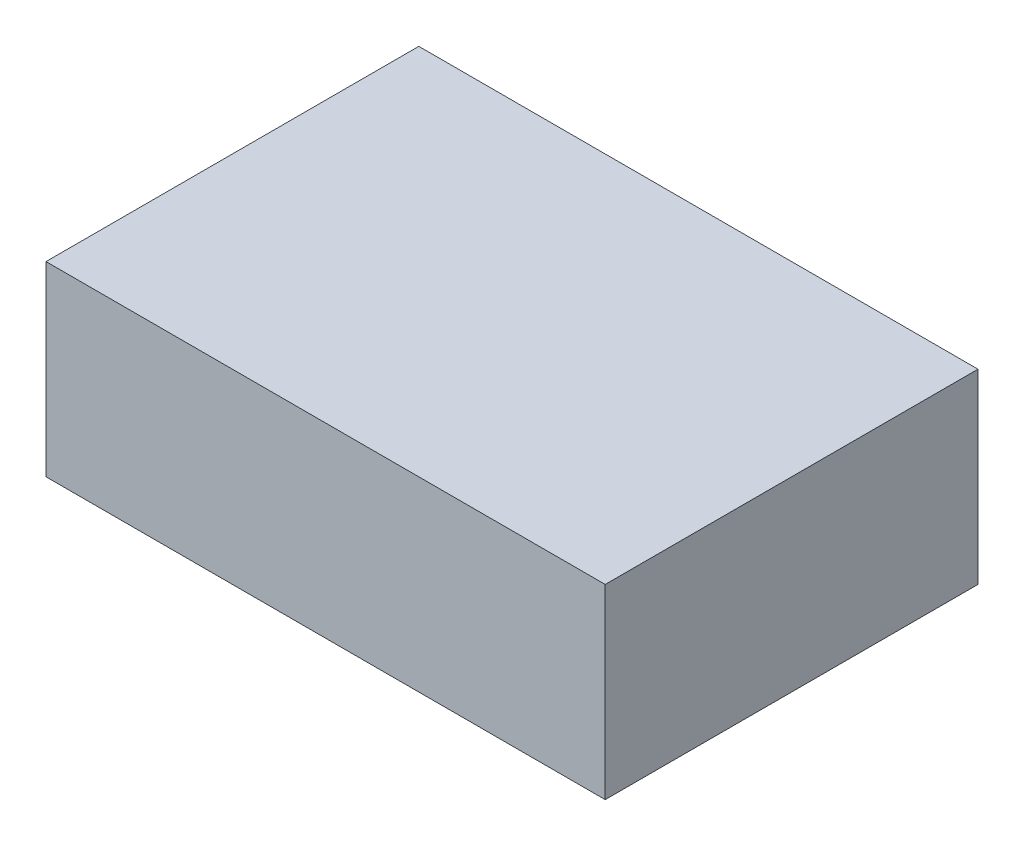
SolidWorks part; units mm, degrees
ref_plane "Front Plane" through (0, 0, 0) normal (0, 0, 1) x (1, 0, 0)
ref_plane "Top Plane" through (0, 0, 0) normal (0, 1, 0) x (1, 0, 0)
ref_plane "Right Plane" through (0, 0, 0) normal (1, 0, 0) x (0, 0, -1)
sketch "Sketch1" plane through (0, 0, 0) normal (0, 1, 0) x (1, 0, 0)
  line L1 (75, -50) -> (-75, -50)
  line L2 (75, -50) -> (75, 50)
  line L3 (75, 50) -> (-75, 50)
  line L4 (-75, -50) -> (-75, 50)
  line L5 (75, -50) -> (-75, 50) construction
  line L6 (75, 50) -> (-75, -50) construction
  point P0 (0, 0)
  dimension "D1" = 150
  dimension "D2" = 100
extrude "Boss-Extrude1" add sketch "Sketch1" along normal blind 50 contours L4 L3 L2 L1
